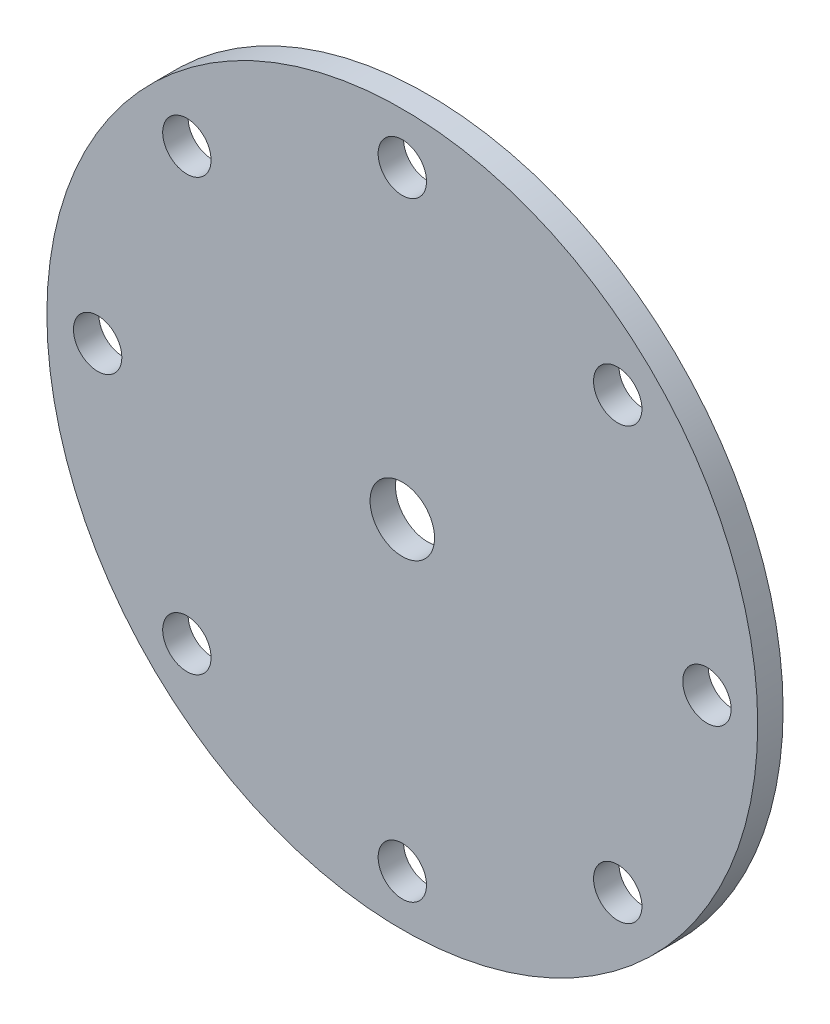
SolidWorks part; units mm, degrees
ref_plane "Front Plane" through (0, 0, 0) normal (0, 0, 1) x (1, 0, 0)
ref_plane "Top Plane" through (0, 0, 0) normal (0, 1, 0) x (1, 0, 0)
ref_plane "Right Plane" through (0, 0, 0) normal (1, 0, 0) x (0, 0, -1)
sketch "Sketch1" plane through (0, 0, 0) normal (0, 0, 1) x (1, 0, 0)
  line L0 (0, 70) -> (0, -70) construction
  line L1 (-70, 0) -> (70, 0) construction
  line L2 (-42.4264, 42.4264) -> (42.4264, -42.4264) construction
  line L3 (-42.4264, -42.4264) -> (42.4264, 42.4264) construction
  circle A0 centre (0, 0) radius 70
  circle A1 centre (0, 0) radius 6.35
  circle A2 centre (0, 60) radius 4.7625
  circle A6 centre (42.4264, 42.4264) radius 4.7625
  circle A7 centre (60, 0) radius 4.7625
  circle A8 centre (42.4264, -42.4264) radius 4.7625
  circle A9 centre (0, -60) radius 4.7625
  circle A10 centre (-42.4264, -42.4264) radius 4.7625
  circle A11 centre (-60, 0) radius 4.7625
  circle A12 centre (-42.4264, 42.4264) radius 4.7625
  dimension "D1" = 140
  dimension "D2" = 12.7
  dimension "D3" = 9.525
  dimension "D6" = 10
  dimension "D4" = 10
  dimension "D5" = 8
extrude "Rotor Disc" add sketch "Sketch1" along normal blind 5
